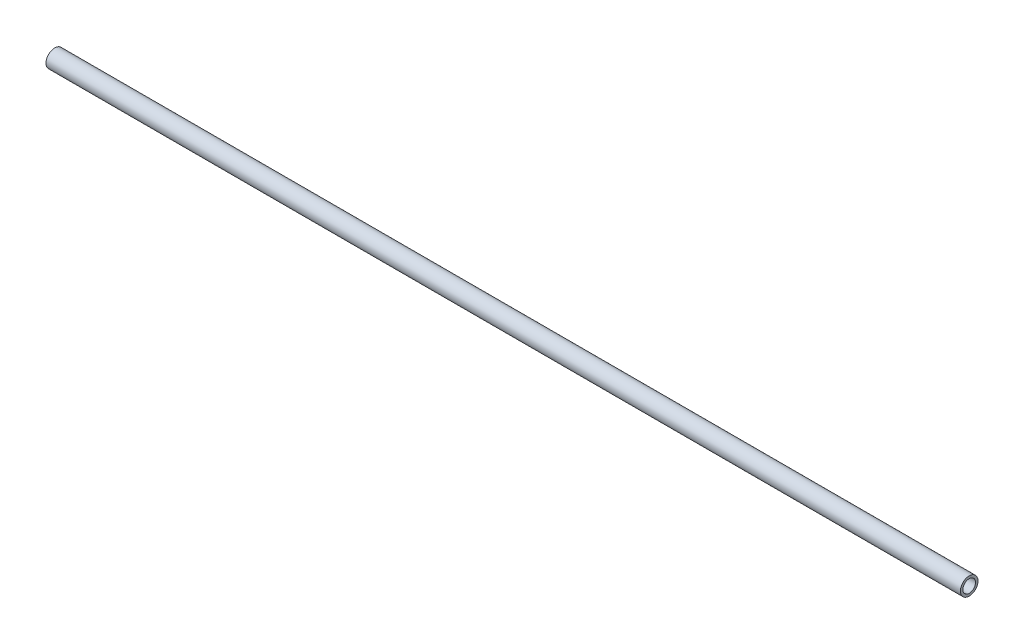
SolidWorks part; units mm, degrees
material "AISI 316 Stainless Steel Sheet (SS)"
ref_plane "Front Plane" through (0, 0, 0) normal (0, 0, 1) x (1, 0, 0)
ref_plane "Top Plane" through (0, 0, 0) normal (0, 1, 0) x (1, 0, 0)
ref_plane "Right Plane" through (0, 0, 0) normal (1, 0, 0) x (0, 0, -1)
sketch "Sketch1" plane through (0, 0, 0) normal (0, 0, 1) x (1, 0, 0)
  line L0 (0, -374.3943) -> (0, -1.5223)
  line L1 (19.05, 17.5277) -> (63.5, 17.5277)
  arc A0 (0, -1.5223) -> (19.05, 17.5277) centre (19.05, -1.5223) cw
  point P6 (0, 17.5277)
  dimension "D3" = 19.05
  dimension "D1" = 63.5
  dimension "D2" = 391.922
ref_plane "Plane1" through (63.5, 17.5277, 0) normal (1, 0, 0) x (0, 0, -1)
sketch "Sketch2" plane through (63.5, 17.5277, 0) normal (1, 0, 0) x (0, 0, -1)
  circle A0 centre (0, 0) radius 3.175
  circle A1 centre (0, 0) radius 2.286
  dimension "D1" = 6.35
  dimension "D2" = 4.572
extrude "Boss-Extrude1" add sketch "Sketch2" along normal mid plane 330.1746
